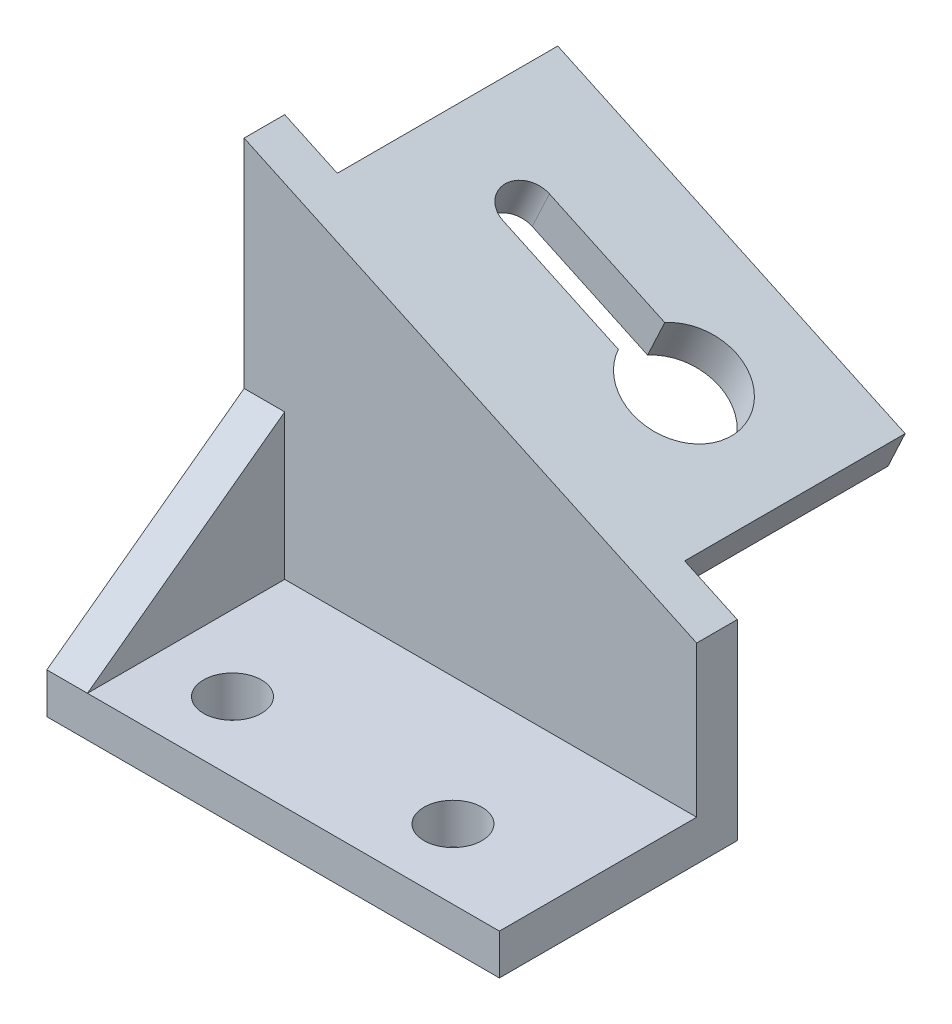
SolidWorks part; units mm, degrees
ref_plane "Front Plane" through (0, 0, 0) normal (0, 0, 1) x (1, 0, 0)
ref_plane "Top Plane" through (0, 0, 0) normal (0, 1, 0) x (1, 0, 0)
ref_plane "Right Plane" through (0, 0, 0) normal (1, 0, 0) x (0, 0, -1)
sketch "Sketch1" plane through (0, 0, 0) normal (0, 0, 1) x (1, 0, 0)
  line L0 (39, 16.5) -> (-39, 52.872)
  line L2 (-39, 16.5) -> (-39, -16.5)
  line L3 (-39, -16.5) -> (39, -16.5)
  line L4 (39, 16.5) -> (39, -16.5)
  line L5 (-39, 16.5) -> (39, -16.5) construction
  line L6 (-39, -16.5) -> (39, 16.5) construction
  line L7 (-39, 16.5) -> (-39, 52.872)
  point P0 (0, 0)
  dimension "D1" = 33
  dimension "D2" = 78
extrude "Boss-Extrude1" add sketch "Sketch1" along normal blind 7
sketch "Sketch2" plane through (0, 0, 0) normal (0, 0, -1) x (-1, 0, 0)
  line L0 (-39, 16.5) -> (39, 52.872) construction
  line L1 (-29.9369, 20.7262) -> (29.9369, 48.6458)
  line L2 (-29.9369, 20.7262) -> (-26.9786, 14.382)
  line L3 (29.9369, 48.6458) -> (32.8952, 42.3017)
  line L4 (-26.9786, 14.382) -> (32.8952, 42.3017)
  point P0 (-29.9369, 20.7262)
  point P1 (29.9369, 48.6458)
  point P4 (-39, 16.5)
  point P5 (39, 52.872)
  dimension "D1" = 10
  dimension "D2" = 10
  dimension "D3" = 7
extrude "Boss-Extrude2" add sketch "Sketch2" along normal blind 38
sketch "Sketch3" plane through (13.2855, 28.4909, 0) normal (0.4226, 0.9063, 0) x (0.9063, -0.4226, 0)
  line L1 (-31.6272, 22) -> (-9.6895, 22)
  line L2 (-31.6272, 14) -> (-9.6895, 14)
  arc A0 (-31.6272, 22) -> (-31.6272, 14) centre (-31.6272, 18) ccw
  arc A2 (-9.6895, 14) -> (-9.6895, 22) centre (-1.6272, 18) ccw
  point P2 (-16.6272, 18)
  dimension "D5" = 18
  dimension "D1" = 8
extrude "Cut-Extrude1" cut sketch "Sketch3" against normal blind 48
sketch "Sketch4" plane through (0, 0, 7) normal (0, 0, 1) x (1, 0, 0)
  line L0 (39, -16.5) -> (39, 16.5) construction
  line L1 (-39, -16.5) -> (39, -16.5)
  line L2 (-39, -16.5) -> (-39, -9.5)
  line L3 (-39, -9.5) -> (39, -9.5)
  line L4 (39, -16.5) -> (39, -9.5)
  dimension "D1" = 7
extrude "Boss-Extrude3" add sketch "Sketch4" along normal blind 34
sketch "Sketch5" plane through (-39, 0, 0) normal (-1, 0, 0) x (0, 0, 1)
  line L0 (7, -9.5) -> (7, 15.5)
  line L1 (7, 52.872) -> (7, -9.5) construction
  line L2 (7, 15.5) -> (41, -9.5)
  line L3 (41, -9.5) -> (7, -9.5)
  dimension "D1" = 25
extrude "Boss-Extrude4" add sketch "Sketch5" against normal blind 7
sketch "Sketch6" plane through (0, -9.5, 0) normal (0, 1, 0) x (1, 0, 0)
  line L0 (39, -41) -> (-32, -41) construction
  line L1 (-39, -41) -> (-39, -7) construction
  line L2 (39, -41) -> (39, -7) construction
  circle A0 centre (-19, -29) radius 5
  circle A1 centre (19, -29) radius 5
  point P8 (0, 0)
  dimension "D1" = 10
  dimension "D2" = 10
  dimension "D3" = 12
  dimension "D4" = 20
  dimension "D5" = 20
extrude "Cut-Extrude2" cut sketch "Sketch6" against normal blind 21
